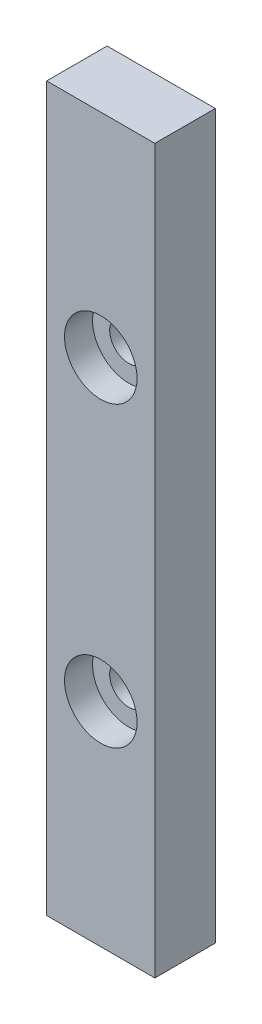
SolidWorks part; units mm, degrees
material "6061-T6 (SS)"
ref_plane "Front Plane" through (0, 0, 0) normal (0, 0, 1) x (1, 0, 0)
ref_plane "Top Plane" through (0, 0, 0) normal (0, 1, 0) x (1, 0, 0)
ref_plane "Right Plane" through (0, 0, 0) normal (1, 0, 0) x (0, 0, -1)
sketch "Sketch1" plane through (0, 0, 0) normal (0, 0, 1) x (1, 0, 0)
  line L1 (0, 0) -> (8.5, 0)
  line L2 (0, 0) -> (0, -56.8)
  line L3 (0, -56.8) -> (8.5, -56.8)
  line L4 (8.5, 0) -> (8.5, -56.8)
  dimension "D1" = 56.8
  dimension "D2" = 8.5
extrude "Boss-Extrude1" add sketch "Sketch1" along normal blind 4.75
sketch "Sketch3" plane through (0, 0, 4.75) normal (0, 0, 1) x (1, 0, 0)
  line L0 (8.5, 0) -> (0, 0) construction
  line L2 (0, -56.8) -> (8.5, -56.8) construction
  line L4 (8.5, -56.8) -> (8.5, 0) construction
  point P9 (4.25, -16.7)
  point P10 (4.25, -40.1)
  dimension "D1" = 16.7
  dimension "D2" = 16.7
  dimension "D3" = 4.25
  dimension "D4" = 4.25
hole_wizard "Ø3.0mm Dowel Hole1" positions "Sketch4" profile "Sketch5" hole size "Ø3.0" standard "ANSI Metric"
sketch "Sketch4" plane through (0, 0, 4.75) normal (0, 0, 1) x (1, 0, 0)
  point P0 (4.25, -16.7)
  point P3 (4.25, -40.1)
sketch "Sketch5" plane through (4.25, -16.7, 4.75) normal (1, 0, 0) x (0, -1, 0)
  line L0 (0, 0) -> (0, 5.9013)
  line L1 (0, 5.9013) -> (1.5, 5)
  line L2 (1.5, 5) -> (1.5, 0)
  line L5 (1.5, 0) -> (0, 0)
  line L10 (0, 5.9013) -> (-1.5, 5) construction
  line L11 (0, -6.35) -> (0, 107.95) construction
  dimension "Hole Dia." = 3
  dimension "Hole Depth" = 5
  dimension "Drill Angle" = 118
sketch "Sketch6" plane through (0, 0, 4.75) normal (0, 0, 1) x (1, 0, 0)
  circle A0 centre (4.25, -16.7) radius 2.85
  circle A1 centre (4.25, -40.1) radius 2.85
  dimension "D1" = 5.7
extrude "Cut-Extrude1" cut sketch "Sketch6" against normal blind 2.2
